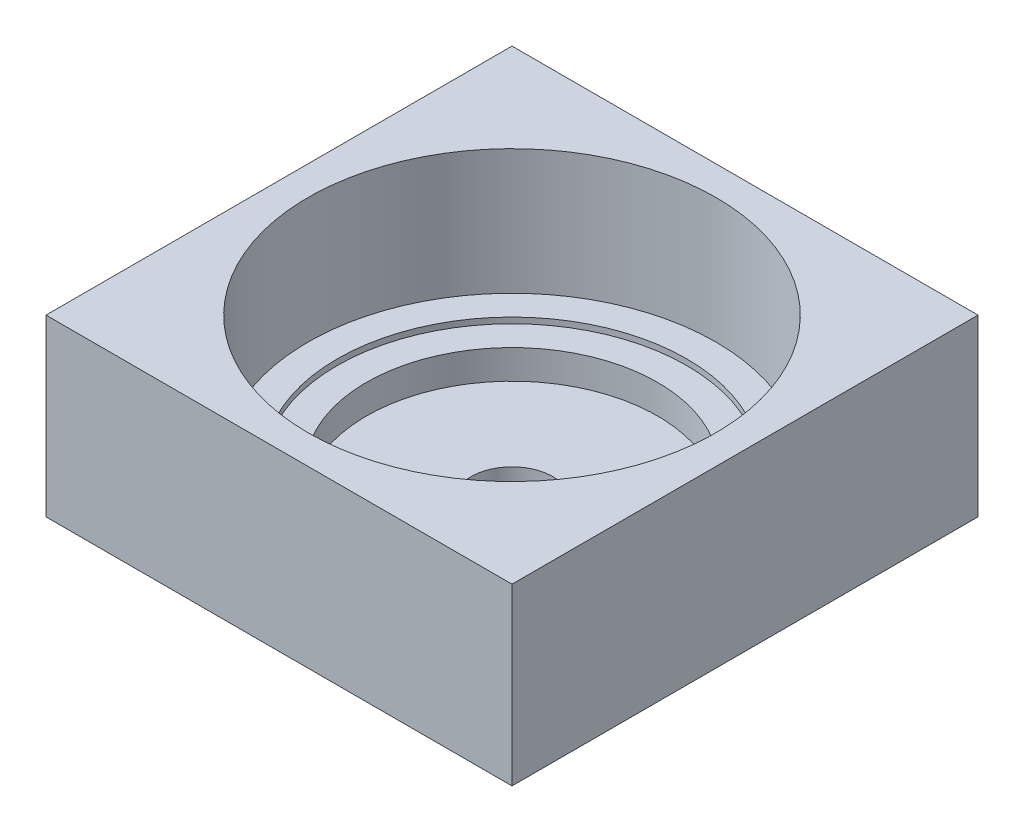
SolidWorks part; units mm, degrees
ref_plane "前基準面" through (0, 0, 0) normal (0, 0, 1) x (1, 0, 0)
ref_plane "上基準面" through (0, 0, 0) normal (0, 1, 0) x (1, 0, 0)
ref_plane "右基準面" through (0, 0, 0) normal (1, 0, 0) x (0, 0, -1)
sketch "草圖1" plane through (0, 0, 0) normal (0, 1, 0) x (1, 0, 0)
  line L1 (-80, -80) -> (80, -80)
  line L2 (-80, -80) -> (-80, 80)
  line L3 (-80, 80) -> (80, 80)
  line L4 (80, -80) -> (80, 80)
  line L5 (-80, -80) -> (80, 80) construction
  line L6 (-80, 80) -> (80, -80) construction
  point P0 (0, 0)
  dimension "D1" = 160
  dimension "D2" = 160
extrude "填料-伸長1" add sketch "草圖1" along normal blind 60
sketch "草圖2" plane through (0, 0, 0) normal (0, 0, 1) x (1, 0, 0)
  line L0 (0, 77.8894) -> (0, -27.0737) construction
  line L1 (0, 0) -> (14, 0)
  line L2 (-80, 0) -> (80, 0) construction
  line L3 (14, 0) -> (14, 5)
  line L4 (14, 5) -> (50, 5)
  line L5 (50, 5) -> (50, 15)
  line L6 (50, 15) -> (60, 15)
  line L7 (60, 15) -> (60, 17)
  line L8 (60, 17) -> (70, 17)
  line L9 (70, 17) -> (70, 60)
  line L10 (-80, 60) -> (80, 60) construction
  line L11 (0, 0) -> (0, 60)
  line L12 (0, 60) -> (70, 60)
  dimension "D1" = 140
  dimension "D2" = 120
  dimension "D3" = 100
  dimension "D4" = 28
  dimension "D5" = 2
  dimension "D6" = 43
  dimension "D7" = 5
revolve "除料-旋轉1" cut sketch "草圖2" angle 360 about L0
